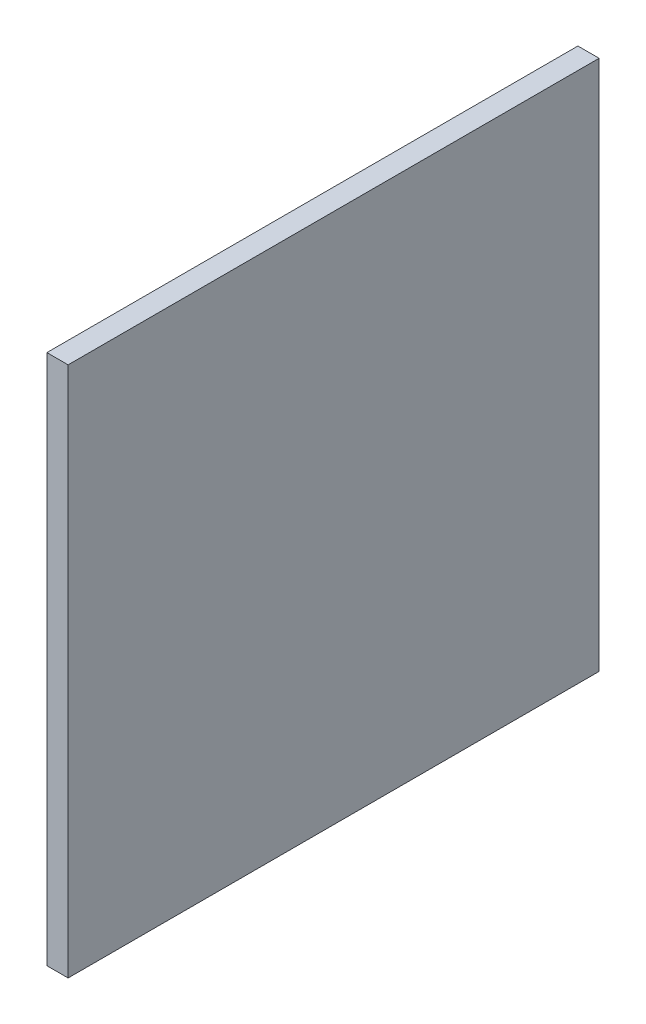
SolidWorks part; units mm, degrees
ref_plane "前视基准面" through (0, 0, 0) normal (0, 0, 1) x (1, 0, 0)
ref_plane "上视基准面" through (0, 0, 0) normal (0, 1, 0) x (1, 0, 0)
ref_plane "右视基准面" through (0, 0, 0) normal (1, 0, 0) x (0, 0, -1)
sketch "草图1" plane through (0, 0, 0) normal (1, 0, 0) x (0, 0, -1)
  line L1 (250, 250) -> (-250, 250)
  line L2 (250, 250) -> (250, -250)
  line L3 (250, -250) -> (-250, -250)
  line L4 (-250, 250) -> (-250, -250)
  line L5 (250, 250) -> (-250, -250) construction
  line L6 (250, -250) -> (-250, 250) construction
  point P0 (0, 0)
  dimension "D1" = 500
extrude "凸台-拉伸1" add sketch "草图1" along normal blind 20
